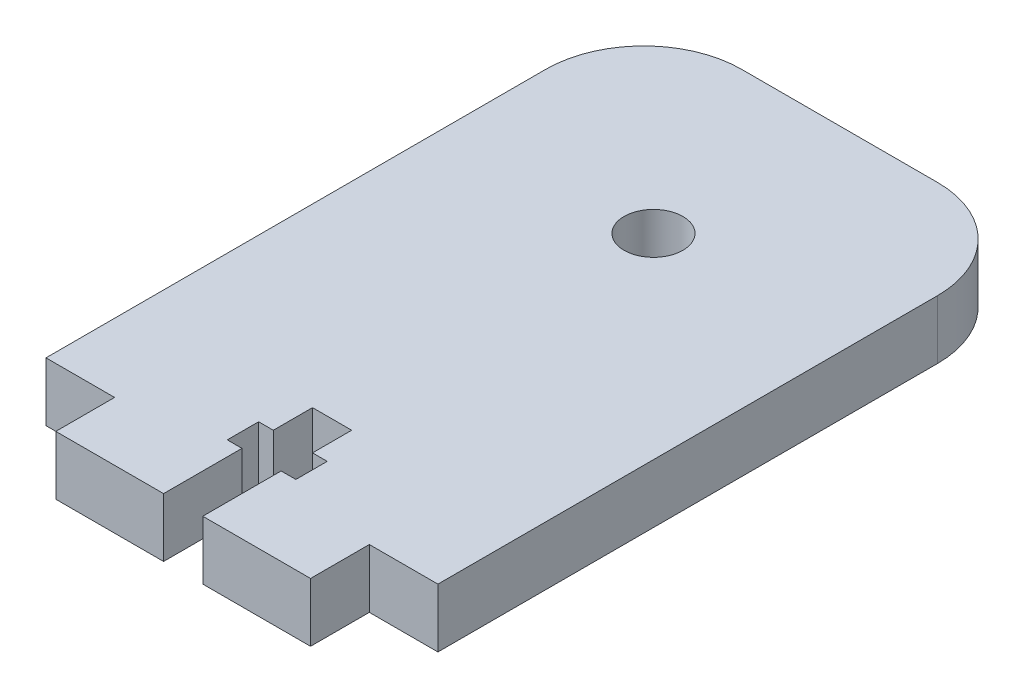
SolidWorks part; units mm, degrees
ref_plane "Front Plane" through (0, 0, 0) normal (0, 0, 1) x (1, 0, 0)
ref_plane "Top Plane" through (0, 0, 0) normal (0, 1, 0) x (1, 0, 0)
ref_plane "Right Plane" through (0, 0, 0) normal (1, 0, 0) x (0, 0, -1)
sketch "Sketch1" plane through (0, 0, 0) normal (0, 1, 0) x (1, 0, 0)
  line L0 (-13.5202, -4) -> (-2.5202, -4) construction
  line L1 (-10.5202, 63) -> (9.4798, 63)
  line L5 (-2.5202, -4) -> (-2.5202, 4)
  line L6 (-2.5202, 4) -> (-4.0202, 4)
  line L11 (-0.5202, 63) -> (-0.5202, 44) construction
  line L12 (-4.0202, 4) -> (-4.0202, 7.2)
  line L13 (-13.5202, 2) -> (-20.5202, 2)
  line L14 (12.4798, 2) -> (19.4798, 2)
  line L16 (-20.5202, 53) -> (-20.5202, 2)
  line L17 (19.4798, 53) -> (19.4798, 2)
  line L30 (-4.0202, 7.2) -> (-2.5202, 7.2)
  line L36 (-2.5202, 7.2) -> (-2.5202, 11.2)
  line L38 (-13.5202, 2) -> (-13.5202, -4)
  line L39 (-13.5202, -4) -> (-2.5202, -4)
  line L40 (12.4798, 2) -> (12.4798, -4)
  line L41 (-2.5202, 11.2) -> (1.4798, 11.2)
  line L42 (1.4798, 11.2) -> (1.4798, 7.2)
  line L43 (1.4798, 7.2) -> (2.9798, 7.2)
  line L44 (2.9798, 7.2) -> (2.9798, 4)
  line L45 (2.9798, 4) -> (1.4798, 4)
  line L46 (1.4798, 4) -> (1.4798, -4)
  line L47 (1.4798, -4) -> (12.4798, -4)
  arc A0 (9.4798, 63) -> (19.4798, 53) centre (9.4798, 53) cw
  arc A1 (-10.5202, 63) -> (-20.5202, 53) centre (-10.5202, 53) ccw
  circle A3 centre (-0.5202, 44) radius 3
  point P0 (-0.5202, 3)
  dimension "D1" = 19
  dimension "D2" = 6
  dimension "D3" = 10
  dimension "D4" = 61
  dimension "D5" = 40
  dimension "D6" = 7
  dimension "D7" = 7
  dimension "D8" = 26
  dimension "D9" = 6
  dimension "D10" = 4
  dimension "D11" = 11
  dimension "D12" = 8
  dimension "D13" = 1.5
  dimension "D14" = 3.2
  dimension "D15" = 1.5
  dimension "D16" = 4
extrude "Boss-Extrude2" add sketch "Sketch1" against normal blind 6
